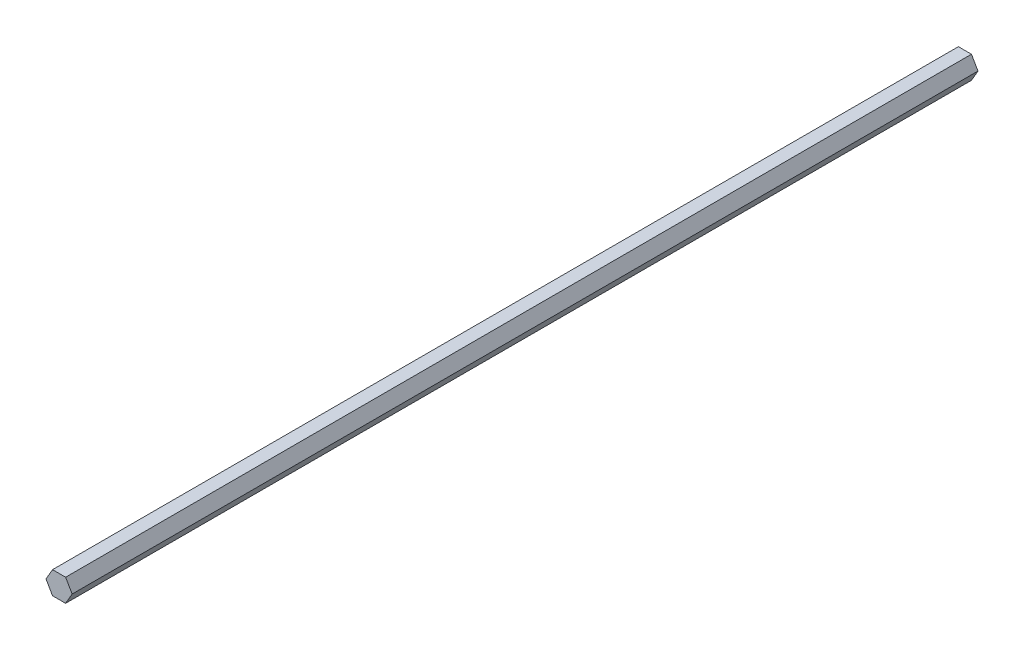
SolidWorks part; units mm, degrees
ref_plane "Front Plane" through (0, 0, 0) normal (0, 0, 1) x (1, 0, 0)
ref_plane "Top Plane" through (0, 0, 0) normal (0, 1, 0) x (1, 0, 0)
ref_plane "Right Plane" through (0, 0, 0) normal (1, 0, 0) x (0, 0, -1)
sketch "Sketch1" plane through (0, 0, 0) normal (0, 0, 1) x (1, 0, 0)
  line L1 (7.3323, 0) -> (3.6662, 6.35)
  line L2 (3.6662, 6.35) -> (-3.6662, 6.35)
  line L3 (-3.6662, 6.35) -> (-7.3323, 0)
  line L4 (-7.3323, 0) -> (-3.6662, -6.35)
  line L5 (-3.6662, -6.35) -> (3.6662, -6.35)
  line L6 (3.6662, -6.35) -> (7.3323, 0)
  circle A0 centre (0, 0) radius 6.35 construction
  point P1 (0, 0)
  dimension "D1" = 12.7
extrude "Boss-Extrude1" add sketch "Sketch1" along normal blind 508
